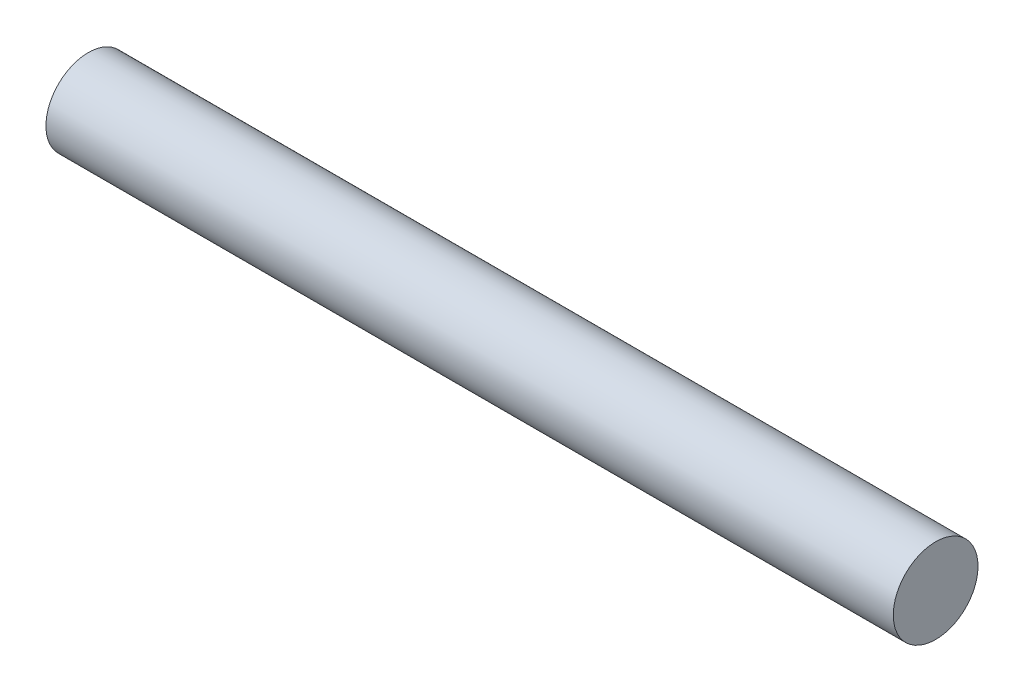
SolidWorks part; units mm, degrees
ref_plane "前视基准面" through (0, 0, 0) normal (0, 0, 1) x (1, 0, 0)
ref_plane "上视基准面" through (0, 0, 0) normal (0, 1, 0) x (1, 0, 0)
ref_plane "右视基准面" through (0, 0, 0) normal (1, 0, 0) x (0, 0, -1)
sketch "草图1" plane through (0, 0, 0) normal (1, 0, 0) x (0, 0, -1)
  circle A0 centre (0, 0) radius 4
  dimension "D1" = 8
extrude "凸台-拉伸1" add sketch "草图1" along normal blind 80
